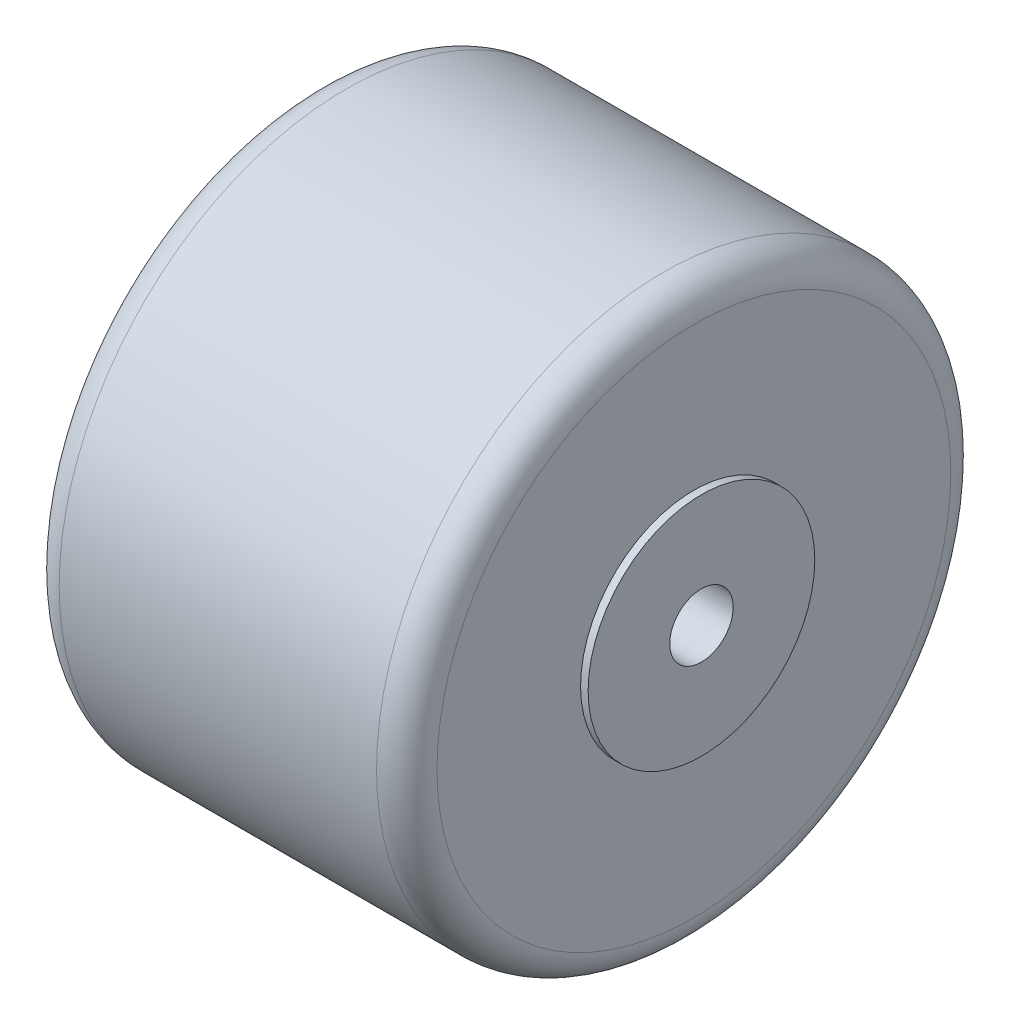
SolidWorks part; units mm, degrees
ref_plane "Ebene vorne" through (0, 0, 0) normal (0, 0, 1) x (1, 0, 0)
ref_plane "Ebene oben" through (0, 0, 0) normal (0, 1, 0) x (1, 0, 0)
ref_plane "Ebene rechts" through (0, 0, 0) normal (1, 0, 0) x (0, 0, -1)
sketch "Skizze1" plane through (0, 0, 0) normal (0, 0, 1) x (1, 0, 0)
  line L0 (0, 0) -> (29.4602, 0) construction
  line L1 (0, 0) -> (0, 7.5)
  line L2 (0, 0) -> (26, 0)
  line L4 (0.5, 19) -> (25.5, 19)
  line L5 (0, 7.5) -> (0.5, 7.5)
  line L6 (0.5, 7.5) -> (0.5, 19)
  line L7 (26, 0) -> (26, 7.5)
  line L8 (26, 7.5) -> (25.5, 7.5)
  line L9 (25.5, 7.5) -> (25.5, 19)
  point P9 (13, 19)
  point P10 (13, 0)
  dimension "D1" = 38
  dimension "D2" = 26
  dimension "D3" = 0.5
  dimension "D4" = 15
revolve "Rotation1" add sketch "Skizze1" angle 360 about L0
hole_wizard "M5 Gewindebohrung1" positions "3D-Skizze1" profile "Skizze2" tap size "M5" standard "DIN"
sketch3d "3D-Skizze1"
  line L0 (26, 0, 0) -> (25.5, 0, 0) construction
  point P0 (26, 0, 0)
  point P4 (0, 0, 0)
  point P7 (0, 0, 0)
sketch "Skizze2" plane through (26, 0, 0) normal (0, 1, 0) x (0, 0, -1)
  line L0 (0, 0) -> (0, 13.2618)
  line L1 (0, 13.2618) -> (2.1, 12)
  line L2 (2.1, 12) -> (2.1, 0)
  line L5 (2.1, 0) -> (0, 0)
  line L10 (0, 13.2618) -> (-2.1, 12) construction
  line L11 (0, -6.35) -> (0, 107.95) construction
  dimension "Bohrerdurchmesser" = 4.2
  dimension "Bohrungstiefe" = 12
  dimension "Spitzenwinkel" = 118
cosmetic thread "Bohrungsgewinde3"
hole_wizard "M5 Gewindebohrung2" positions "Skizze3" profile "Skizze4" tap size "M5" standard "DIN"
sketch "Skizze3" plane through (0, 0, 0) normal (-1, 0, 0) x (0, 0, 1)
  point P0 (0, 0)
sketch "Skizze4" plane through (0, 0, 0) normal (0, 1, 0) x (0, 0, 1)
  line L0 (0, 0) -> (0, 13.2618)
  line L1 (0, 13.2618) -> (2.1, 12)
  line L2 (2.1, 12) -> (2.1, 0)
  line L5 (2.1, 0) -> (0, 0)
  line L10 (0, 13.2618) -> (-2.1, 12) construction
  line L11 (0, -6.35) -> (0, 107.95) construction
  dimension "Bohrerdurchmesser" = 4.2
  dimension "Bohrungstiefe" = 12
  dimension "Spitzenwinkel" = 118
cosmetic thread "Bohrungsgewinde4"
fillet "Verrundung1" radius 2 2 edges at (25.5, 0, 19) (0.5, 0, 19)
